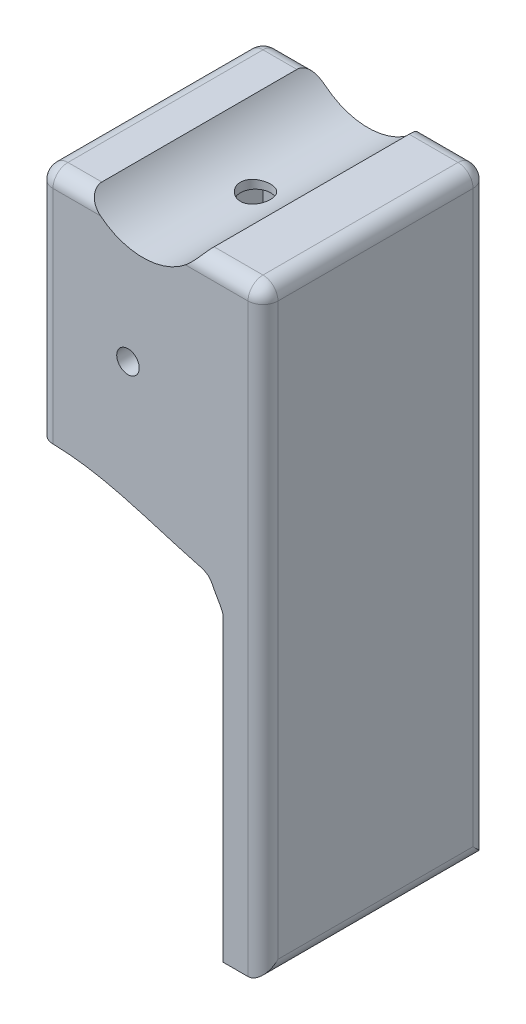
SolidWorks part; units mm, degrees
ref_plane "Alzado" through (0, 0, 0) normal (0, 0, 1) x (1, 0, 0)
ref_plane "Planta" through (0, 0, 0) normal (0, 1, 0) x (1, 0, 0)
ref_plane "Vista lateral" through (0, 0, 0) normal (1, 0, 0) x (0, 0, -1)
sketch "Croquis1" plane through (0, 0, 0) normal (0, 0, 1) x (1, 0, 0)
  line L1 (-39.9466, 14.3416) -> (-11.9466, 14.3416)
  line L2 (-39.9466, 14.3416) -> (-39.9466, -15.6584)
  line L3 (-39.9466, -15.6584) -> (-11.9466, -15.6584)
  line L4 (-11.9466, 14.3416) -> (-11.9466, -15.6584)
  dimension "D1" = 28
  dimension "D2" = 30
extrude "Saliente-Extruir1" add sketch "Croquis1" along normal blind 30
sketch "Croquis2" plane through (0, -15.6584, 0) normal (0, -1, 0) x (1, 0, 0)
  line L0 (-39.9466, 30) -> (-11.9466, 30) construction
  line L1 (-36.9466, 27) -> (-14.9466, 27)
  line L2 (-36.9466, 27) -> (-36.9466, 3)
  line L3 (-36.9466, 3) -> (-14.9466, 3)
  line L4 (-14.9466, 27) -> (-14.9466, 3)
  line L5 (-39.9466, 30) -> (-39.9466, 0) construction
  line L6 (-11.9466, 30) -> (-11.9466, 0) construction
  line L7 (-39.9466, 0) -> (-11.9466, 0) construction
  dimension "D1" = 3
  dimension "D2" = 3
  dimension "D3" = 3
  dimension "D4" = 3
extrude "Cortar-Extruir1" cut sketch "Croquis2" against normal blind 25
sketch "Croquis3" plane through (0, 9.3416, 0) normal (0, -1, 0) x (1, 0, 0)
  line L0 (-14.9466, 27) -> (-36.9466, 3) construction
  circle A0 centre (-25.9466, 15) radius 2
  dimension "D1" = 4
sketch "Croquis5" plane through (0, 0, 30) normal (0, 0, 1) x (1, 0, 0)
  line L0 (-39.9466, 14.3416) -> (-34.9466, 14.3416) construction
  line L1 (-11.9466, 14.3416) -> (-39.9466, 14.3416) construction
  line L2 (-11.9466, 14.3416) -> (-16.9466, 14.3416) construction
  line L4 (-16.9466, 14.3416) -> (-16.9466, 19.3416) construction
  line L5 (-34.9466, 14.3416) -> (-34.9466, 19.3416) construction
  line L6 (-18.4633, 14.3416) -> (-33.4299, 14.3416)
  arc A2 (-18.4633, 14.3416) -> (-33.4299, 14.3416) centre (-25.9466, 19.3416) cw
  dimension "D1" = 5
  dimension "D2" = 5
extrude "Cortar-Extruir3" cut sketch "Croquis5" against normal up to vertex
extrude "Cortar-Extruir4" cut sketch "Croquis3" against normal up to vertex (5 mm away)
sketch "Croquis6" plane through (0, 0, 30) normal (0, 0, 1) x (1, 0, 0)
  line L0 (-39.9466, 14.3416) -> (-39.9466, -15.6584) construction
  line L1 (-39.9466, -15.6584) -> (-11.9466, -15.6584) construction
  circle A0 centre (-27.9466, -2.6584) radius 1.5
  dimension "D1" = 12
  dimension "D2" = 13
extrude "Cortar-Extruir5" cut sketch "Croquis6" against normal up to vertex
sketch "Croquis8" plane through (-11.9466, 0, 0) normal (1, 0, 0) x (0, 0, -1)
  line L1 (-30, 14.3416) -> (0, 14.3416)
  line L2 (-30, 14.3416) -> (-30, -63.6584)
  line L3 (-30, -63.6584) -> (0, -63.6584)
  line L4 (0, 14.3416) -> (0, -63.6584)
  dimension "D1" = 78
extrude "Saliente-Extruir2" add sketch "Croquis8" along normal blind 2
sketch "Croquis9" plane through (0, -15.6584, 0) normal (0, -1, 0) x (1, 0, 0)
  line L0 (-36.9466, 3) -> (-14.9466, 3) construction
  line L1 (-11.9466, 0) -> (-15.2466, 0)
  line L2 (-11.9466, 0) -> (-11.9466, 3)
  line L3 (-11.9466, 3) -> (-15.2466, 3)
  line L4 (-15.2466, 0) -> (-15.2466, 3)
  line L5 (-14.9466, 27) -> (-36.9466, 27) construction
  line L6 (-11.9466, 30) -> (-15.2466, 30)
  line L7 (-11.9466, 30) -> (-11.9466, 27)
  line L8 (-11.9466, 27) -> (-15.2466, 27)
  line L9 (-15.2466, 30) -> (-15.2466, 27)
  dimension "D1" = 3.3
extrude "Saliente-Extruir3" add sketch "Croquis9" along normal up to vertex (48 mm away)
sketch "Croquis10" plane through (-9.9466, 0, 0) normal (1, 0, 0) x (0, 0, -1)
  line L1 (0, -63.6584) -> (-30, -63.6584)
  line L2 (0, -63.6584) -> (0, -65.6584)
  line L3 (0, -65.6584) -> (-30, -65.6584)
  line L4 (-30, -63.6584) -> (-30, -65.6584)
  dimension "D1" = 2
extrude "Saliente-Extruir4" add sketch "Croquis10" against normal up to vertex (5.3 mm away)
sketch "Croquis11" plane through (-11.9466, 0, 0) normal (-1, 0, 0) x (0, 0, 1)
  line L1 (27, -63.6584) -> (3, -63.6584)
  line L2 (27, -63.6584) -> (27, -15.6584)
  line L3 (27, -15.6584) -> (3, -15.6584)
  line L4 (3, -63.6584) -> (3, -15.6584)
extrude "Cortar-Extruir6" cut sketch "Croquis11" against normal blind 1
sketch "Croquis12" plane through (0, 0, 30) normal (0, 0, 1) x (1, 0, 0)
  line L0 (-15.2466, -15.6584) -> (-15.2466, -24.6584)
  line L1 (-15.2466, -65.6584) -> (-15.2466, -15.6584) construction
  line L3 (-15.2466, -15.6584) -> (-39.9466, -15.6584)
  line L5 (-39.9466, -15.6584) -> (-39.9466, -17.1584)
  line L6 (-15.2466, -24.6584) -> (-15.2466, -25.6584)
  spline S2 degree 3 poles (-15.2466, -25.6584) (-15.4543, -24.7844) (-16.2767, -23.7693) (-17.0604, -21.8195) (-25.7428, -19.638) (-31.7192, -16.941) (-39.9466, -17.1584) knots 0 0 0 0 0.094483 0.14565 0.216241 1 1 1 1
  dimension "D1" = 1.5
  dimension "D2" = 9
extrude "Saliente-Extruir5" add sketch "Croquis12" against normal up to vertex (3 mm away)
ref_plane "Plano1" through (0, 0, 15) normal (0, 0, -1) x (-1, 0, 0)
mirror "Simetría2" about plane through (0, 0, 15) normal (0, 0, -1) of "Saliente-Extruir5"
fillet "Redondeo2" radius 2 13 edges at (-14.205, 14.3416, 30) (-36.6883, 14.3416, 0) (-36.6883, 14.3416, 30) (-39.9466, -1.4084, 30) (-14.205, 14.3416, 0) (-9.9466, -25.6584, 30) (-9.9466, -25.6584, 0) (-9.9466, 14.3416, 15) (-39.9466, -1.4084, 0) (-39.9466, 14.3416, 15) (-9.9466, -65.6584, 15)
